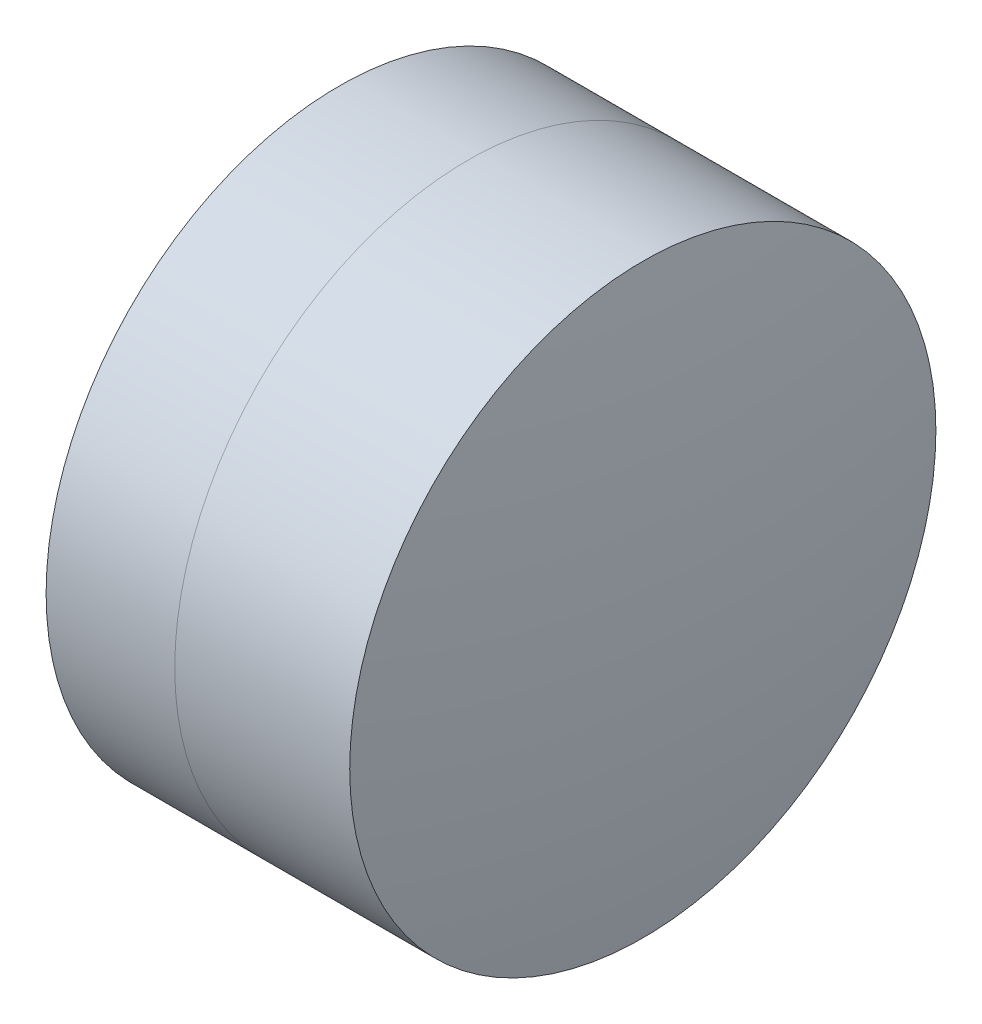
SolidWorks part; units mm, degrees
ref_plane "前视基准面" through (0, 0, 0) normal (0, 0, 1) x (1, 0, 0)
ref_plane "上视基准面" through (0, 0, 0) normal (0, 1, 0) x (1, 0, 0)
ref_plane "右视基准面" through (0, 0, 0) normal (1, 0, 0) x (0, 0, -1)
sketch "草图1" plane through (0, 0, 0) normal (0, 1, 0) x (1, 0, 0)
  line L0 (-0.8161, 0) -> (11.7646, 0) construction
  line L1 (6.1731, -3.15) -> (7.5556, -3.15)
  line L2 (6.1731, 3.15) -> (7.5556, 3.15)
  arc A0 (7.5556, -3.15) -> (7.5556, 3.15) centre (1.0946, 0) ccw
  arc A1 (6.1731, 3.15) -> (6.1731, -3.15) centre (16.0426, 0) ccw
  point P4 (11.7646, 0)
  point P10 (5.6826, 0)
  point P11 (8.2826, 0)
  dimension "D3" = 10.36
  dimension "D4" = 7.188
  dimension "D1" = 3.15
  dimension "D2" = 3.15
  dimension "D5" = 2.6
revolve "旋转1" add sketch "草图1" angle 360 about L0
sketch "草图2" plane through (0, 0, 0) normal (0, 1, 0) x (1, 0, 0)
  line L0 (-0.5519, 0) -> (10.269, 0) construction
  line L2 (7.5556, 3.15) -> (9.4363, 3.15)
  line L3 (7.5556, -3.15) -> (9.4363, -3.15)
  arc A0 (9.4363, -3.15) -> (9.4363, 3.15) centre (-10.5814, 0) ccw
  arc A1 (7.5556, -3.15) -> (7.5556, 3.15) centre (1.0946, 0) ccw construction
  arc A2 (7.5556, -3.15) -> (7.5556, 3.15) centre (1.0946, 0) ccw
  point P4 (8.2826, 0)
  point P8 (9.6826, 0)
  dimension "D1" = 20.264
  dimension "D2" = 1.4
revolve "旋转3" add sketch "草图2" angle 360 about L0
